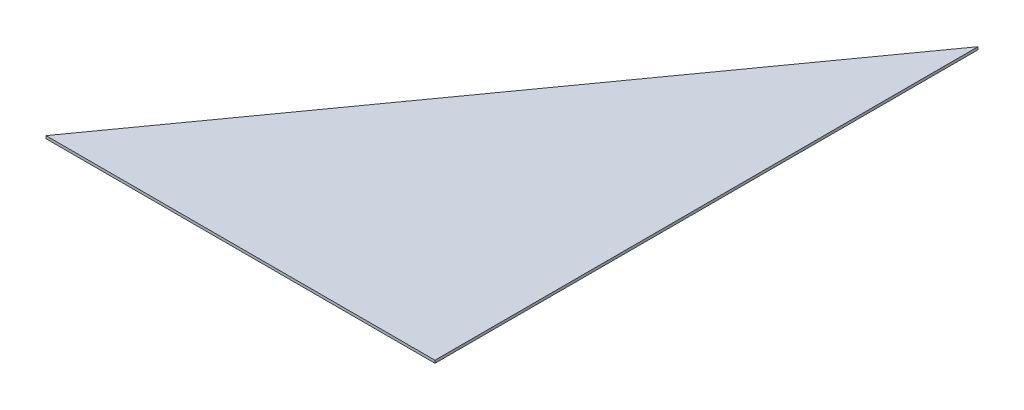
SolidWorks part; units mm, degrees
ref_plane "Front Plane" through (0, 0, 0) normal (0, 0, 1) x (1, 0, 0)
ref_plane "Top Plane" through (0, 0, 0) normal (0, 1, 0) x (1, 0, 0)
ref_plane "Right Plane" through (0, 0, 0) normal (1, 0, 0) x (0, 0, -1)
sketch "Sketch2" plane through (0, 0, 0) normal (0, 1, 0) x (1, 0, 0)
  line L0 (0, 0) -> (228.5279, 319.024)
  line L1 (228.5279, 319.024) -> (228.5279, 0)
  line L2 (228.5279, 0) -> (0, 0)
  dimension "D1" = 319.024
  dimension "D2" = 392.43
extrude "Boss-Extrude1" add sketch "Sketch2" along normal blind 1.5875
